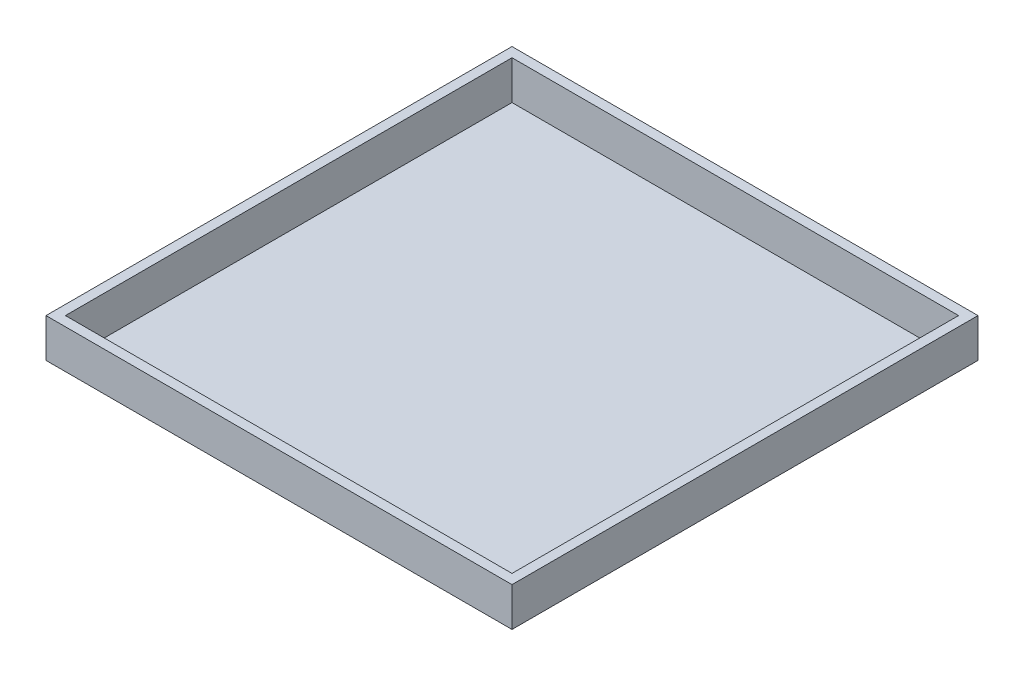
SolidWorks part; units mm, degrees
ref_plane "Front Plane" through (0, 0, 0) normal (0, 0, 1) x (1, 0, 0)
ref_plane "Top Plane" through (0, 0, 0) normal (0, 1, 0) x (1, 0, 0)
ref_plane "Right Plane" through (0, 0, 0) normal (1, 0, 0) x (0, 0, -1)
sketch "Sketch1" plane through (0, 0, 0) normal (0, 1, 0) x (1, 0, 0)
  line L1 (0, 0) -> (2400, 0)
  line L2 (0, 0) -> (0, 2400)
  line L3 (0, 2400) -> (2400, 2400)
  line L4 (2400, 0) -> (2400, 2400)
  dimension "D1" = 2400
  dimension "D2" = 2400
extrude "Boss-Extrude1" add sketch "Sketch1" along normal blind 0.1 contours L4 L3 L2 L1
sketch "Sketch2" plane through (0, 0.1, 0) normal (0, 1, 0) x (1, 0, 0)
  line L0 (50, 2350) -> (50, 50)
  line L1 (0, 2400) -> (2400, 2400)
  line L2 (0, 2400) -> (0, 0)
  line L3 (0, 0) -> (2400, 0)
  line L4 (2400, 2400) -> (2400, 0)
  line L5 (50, 50) -> (2350, 50)
  line L6 (2350, 2350) -> (2350, 50)
  line L7 (50, 2350) -> (2350, 2350)
  dimension "D1" = 50
extrude "Boss-Extrude3" add sketch "Sketch2" along normal blind 200 separate body
sketch "Sketch3" plane through (0, 0.1, 0) normal (0, 1, 0) x (1, 0, 0)
  line L0 (50, 2350) -> (2350, 2350)
  line L1 (2350, 2350) -> (2350, 50)
  line L2 (2350, 50) -> (50, 50)
  line L3 (50, 50) -> (50, 2350)
  line L4 (510, 2350) -> (510, 50)
  line L5 (970, 2350) -> (970, 50)
  line L6 (1430, 2350) -> (1430, 50)
  line L7 (1890, 2350) -> (1890, 50)
  line L8 (2350, 2350) -> (2350, 50)
  line L9 (510, 2350) -> (970, 2350) construction
  line L10 (50, 1890) -> (2350, 1890)
  line L11 (60, 1890) -> (2360, 1890)
  line L12 (60, 1430) -> (2360, 1430)
  line L13 (60, 970) -> (2360, 970)
  line L14 (60, 510) -> (2360, 510)
  line L15 (60, 50) -> (2360, 50)
  line L16 (50, 1430) -> (2350, 1430)
  line L17 (50, 970) -> (2350, 970)
  line L18 (50, 510) -> (2350, 510)
  line L19 (50, 50) -> (2350, 50)
  line L20 (165, 2260) -> (165, 2210)
  line L21 (140, 2235) -> (190, 2235)
  line L22 (280, 2260) -> (280, 2210)
  line L23 (255, 2235) -> (305, 2235)
  line L24 (395, 2260) -> (395, 2210)
  line L25 (370, 2235) -> (420, 2235)
  line L26 (510, 2260) -> (510, 2210)
  line L27 (485, 2235) -> (535, 2235)
  line L28 (625, 2260) -> (625, 2210)
  line L29 (600, 2235) -> (650, 2235)
  line L30 (740, 2260) -> (740, 2210)
  line L31 (715, 2235) -> (765, 2235)
  line L32 (855, 2260) -> (855, 2210)
  line L33 (830, 2235) -> (880, 2235)
  line L34 (970, 2260) -> (970, 2210)
  line L35 (945, 2235) -> (995, 2235)
  line L36 (1085, 2260) -> (1085, 2210)
  line L37 (1060, 2235) -> (1110, 2235)
  line L38 (1200, 2260) -> (1200, 2210)
  line L39 (1175, 2235) -> (1225, 2235)
  line L40 (1315, 2260) -> (1315, 2210)
  line L41 (1290, 2235) -> (1340, 2235)
  line L42 (1430, 2260) -> (1430, 2210)
  line L43 (1405, 2235) -> (1455, 2235)
  line L44 (1545, 2260) -> (1545, 2210)
  line L45 (1520, 2235) -> (1570, 2235)
  line L46 (1660, 2260) -> (1660, 2210)
  line L47 (1635, 2235) -> (1685, 2235)
  line L48 (1775, 2260) -> (1775, 2210)
  line L49 (1750, 2235) -> (1800, 2235)
  line L50 (1890, 2260) -> (1890, 2210)
  line L51 (1865, 2235) -> (1915, 2235)
  line L52 (2005, 2260) -> (2005, 2210)
  line L53 (1980, 2235) -> (2030, 2235)
  line L54 (2120, 2260) -> (2120, 2210)
  line L55 (2095, 2235) -> (2145, 2235)
  line L56 (2235, 2260) -> (2235, 2210)
  line L57 (2210, 2235) -> (2260, 2235)
  line L58 (280, 2145) -> (280, 2095)
  line L59 (255, 2120) -> (305, 2120)
  line L60 (395, 2145) -> (395, 2095)
  line L61 (370, 2120) -> (420, 2120)
  line L62 (510, 2145) -> (510, 2095)
  line L63 (485, 2120) -> (535, 2120)
  line L64 (625, 2145) -> (625, 2095)
  line L65 (600, 2120) -> (650, 2120)
  line L66 (740, 2145) -> (740, 2095)
  line L67 (715, 2120) -> (765, 2120)
  line L68 (855, 2145) -> (855, 2095)
  line L69 (830, 2120) -> (880, 2120)
  line L70 (970, 2145) -> (970, 2095)
  line L71 (945, 2120) -> (995, 2120)
  line L72 (1085, 2145) -> (1085, 2095)
  line L73 (1060, 2120) -> (1110, 2120)
  line L74 (1200, 2145) -> (1200, 2095)
  line L75 (1175, 2120) -> (1225, 2120)
  line L76 (1315, 2145) -> (1315, 2095)
  line L77 (1290, 2120) -> (1340, 2120)
  line L78 (1430, 2145) -> (1430, 2095)
  line L79 (1405, 2120) -> (1455, 2120)
  line L80 (1545, 2145) -> (1545, 2095)
  line L81 (1520, 2120) -> (1570, 2120)
  line L82 (1660, 2145) -> (1660, 2095)
  line L83 (1635, 2120) -> (1685, 2120)
  line L84 (1775, 2145) -> (1775, 2095)
  line L85 (1750, 2120) -> (1800, 2120)
  line L86 (1890, 2145) -> (1890, 2095)
  line L87 (1865, 2120) -> (1915, 2120)
  line L88 (2005, 2145) -> (2005, 2095)
  line L89 (1980, 2120) -> (2030, 2120)
  line L90 (2120, 2145) -> (2120, 2095)
  line L91 (2095, 2120) -> (2145, 2120)
  line L92 (2235, 2145) -> (2235, 2095)
  line L93 (2210, 2120) -> (2260, 2120)
  line L94 (280, 2030) -> (280, 1980)
  line L95 (255, 2005) -> (305, 2005)
  line L96 (395, 2030) -> (395, 1980)
  line L97 (370, 2005) -> (420, 2005)
  line L98 (510, 2030) -> (510, 1980)
  line L99 (485, 2005) -> (535, 2005)
  line L100 (625, 2030) -> (625, 1980)
  line L101 (600, 2005) -> (650, 2005)
  line L102 (740, 2030) -> (740, 1980)
  line L103 (715, 2005) -> (765, 2005)
  line L104 (855, 2030) -> (855, 1980)
  line L105 (830, 2005) -> (880, 2005)
  line L106 (970, 2030) -> (970, 1980)
  line L107 (945, 2005) -> (995, 2005)
  line L108 (1085, 2030) -> (1085, 1980)
  line L109 (1060, 2005) -> (1110, 2005)
  line L110 (1200, 2030) -> (1200, 1980)
  line L111 (1175, 2005) -> (1225, 2005)
  line L112 (1315, 2030) -> (1315, 1980)
  line L113 (1290, 2005) -> (1340, 2005)
  line L114 (1430, 2030) -> (1430, 1980)
  line L115 (1405, 2005) -> (1455, 2005)
  line L116 (1545, 2030) -> (1545, 1980)
  line L117 (1520, 2005) -> (1570, 2005)
  line L118 (1660, 2030) -> (1660, 1980)
  line L119 (1635, 2005) -> (1685, 2005)
  line L120 (1775, 2030) -> (1775, 1980)
  line L121 (1750, 2005) -> (1800, 2005)
  line L122 (1890, 2030) -> (1890, 1980)
  line L123 (1865, 2005) -> (1915, 2005)
  line L124 (2005, 2030) -> (2005, 1980)
  line L125 (1980, 2005) -> (2030, 2005)
  line L126 (2120, 2030) -> (2120, 1980)
  line L127 (2095, 2005) -> (2145, 2005)
  line L128 (2235, 2030) -> (2235, 1980)
  line L129 (2210, 2005) -> (2260, 2005)
  line L130 (280, 1915) -> (280, 1865)
  line L131 (255, 1890) -> (305, 1890)
  line L132 (395, 1915) -> (395, 1865)
  line L133 (370, 1890) -> (420, 1890)
  line L134 (510, 1915) -> (510, 1865)
  line L135 (485, 1890) -> (535, 1890)
  line L136 (625, 1915) -> (625, 1865)
  line L137 (600, 1890) -> (650, 1890)
  line L138 (740, 1915) -> (740, 1865)
  line L139 (715, 1890) -> (765, 1890)
  line L140 (855, 1915) -> (855, 1865)
  line L141 (830, 1890) -> (880, 1890)
  line L142 (970, 1915) -> (970, 1865)
  line L143 (945, 1890) -> (995, 1890)
  line L144 (1085, 1915) -> (1085, 1865)
  line L145 (1060, 1890) -> (1110, 1890)
  line L146 (1200, 1915) -> (1200, 1865)
  line L147 (1175, 1890) -> (1225, 1890)
  line L148 (1315, 1915) -> (1315, 1865)
  line L149 (1290, 1890) -> (1340, 1890)
  line L150 (1430, 1915) -> (1430, 1865)
  line L151 (1405, 1890) -> (1455, 1890)
  line L152 (1545, 1915) -> (1545, 1865)
  line L153 (1520, 1890) -> (1570, 1890)
  line L154 (1660, 1915) -> (1660, 1865)
  line L155 (1635, 1890) -> (1685, 1890)
  line L156 (1775, 1915) -> (1775, 1865)
  line L157 (1750, 1890) -> (1800, 1890)
  line L158 (1890, 1915) -> (1890, 1865)
  line L159 (1865, 1890) -> (1915, 1890)
  line L160 (2005, 1915) -> (2005, 1865)
  line L161 (1980, 1890) -> (2030, 1890)
  line L162 (2120, 1915) -> (2120, 1865)
  line L163 (2095, 1890) -> (2145, 1890)
  line L164 (2235, 1915) -> (2235, 1865)
  line L165 (2210, 1890) -> (2260, 1890)
  line L166 (280, 1800) -> (280, 1750)
  line L167 (255, 1775) -> (305, 1775)
  line L168 (395, 1800) -> (395, 1750)
  line L169 (370, 1775) -> (420, 1775)
  line L170 (510, 1800) -> (510, 1750)
  line L171 (485, 1775) -> (535, 1775)
  line L172 (625, 1800) -> (625, 1750)
  line L173 (600, 1775) -> (650, 1775)
  line L174 (740, 1800) -> (740, 1750)
  line L175 (715, 1775) -> (765, 1775)
  line L176 (855, 1800) -> (855, 1750)
  line L177 (830, 1775) -> (880, 1775)
  line L178 (970, 1800) -> (970, 1750)
  line L179 (945, 1775) -> (995, 1775)
  line L180 (1085, 1800) -> (1085, 1750)
  line L181 (1060, 1775) -> (1110, 1775)
  line L182 (1200, 1800) -> (1200, 1750)
  line L183 (1175, 1775) -> (1225, 1775)
  line L184 (1315, 1800) -> (1315, 1750)
  line L185 (1290, 1775) -> (1340, 1775)
  line L186 (1430, 1800) -> (1430, 1750)
  line L187 (1405, 1775) -> (1455, 1775)
  line L188 (1545, 1800) -> (1545, 1750)
  line L189 (1520, 1775) -> (1570, 1775)
  line L190 (1660, 1800) -> (1660, 1750)
  line L191 (1635, 1775) -> (1685, 1775)
  line L192 (1775, 1800) -> (1775, 1750)
  line L193 (1750, 1775) -> (1800, 1775)
  line L194 (1890, 1800) -> (1890, 1750)
  line L195 (1865, 1775) -> (1915, 1775)
  line L196 (2005, 1800) -> (2005, 1750)
  line L197 (1980, 1775) -> (2030, 1775)
  line L198 (2120, 1800) -> (2120, 1750)
  line L199 (2095, 1775) -> (2145, 1775)
  line L200 (2235, 1800) -> (2235, 1750)
  line L201 (2210, 1775) -> (2260, 1775)
  line L202 (280, 1685) -> (280, 1635)
  line L203 (255, 1660) -> (305, 1660)
  line L204 (395, 1685) -> (395, 1635)
  line L205 (370, 1660) -> (420, 1660)
  line L206 (510, 1685) -> (510, 1635)
  line L207 (485, 1660) -> (535, 1660)
  line L208 (625, 1685) -> (625, 1635)
  line L209 (600, 1660) -> (650, 1660)
  line L210 (740, 1685) -> (740, 1635)
  line L211 (715, 1660) -> (765, 1660)
  line L212 (855, 1685) -> (855, 1635)
  line L213 (830, 1660) -> (880, 1660)
  line L214 (970, 1685) -> (970, 1635)
  line L215 (945, 1660) -> (995, 1660)
  line L216 (1085, 1685) -> (1085, 1635)
  line L217 (1060, 1660) -> (1110, 1660)
  line L218 (1200, 1685) -> (1200, 1635)
  line L219 (1175, 1660) -> (1225, 1660)
  line L220 (1315, 1685) -> (1315, 1635)
  line L221 (1290, 1660) -> (1340, 1660)
  line L222 (1430, 1685) -> (1430, 1635)
  line L223 (1405, 1660) -> (1455, 1660)
  line L224 (1545, 1685) -> (1545, 1635)
  line L225 (1520, 1660) -> (1570, 1660)
  line L226 (1660, 1685) -> (1660, 1635)
  line L227 (1635, 1660) -> (1685, 1660)
  line L228 (1775, 1685) -> (1775, 1635)
  line L229 (1750, 1660) -> (1800, 1660)
  line L230 (1890, 1685) -> (1890, 1635)
  line L231 (1865, 1660) -> (1915, 1660)
  line L232 (2005, 1685) -> (2005, 1635)
  line L233 (1980, 1660) -> (2030, 1660)
  line L234 (2120, 1685) -> (2120, 1635)
  line L235 (2095, 1660) -> (2145, 1660)
  line L236 (2235, 1685) -> (2235, 1635)
  line L237 (2210, 1660) -> (2260, 1660)
  line L238 (280, 1570) -> (280, 1520)
  line L239 (255, 1545) -> (305, 1545)
  line L240 (395, 1570) -> (395, 1520)
  line L241 (370, 1545) -> (420, 1545)
  line L242 (510, 1570) -> (510, 1520)
  line L243 (485, 1545) -> (535, 1545)
  line L244 (625, 1570) -> (625, 1520)
  line L245 (600, 1545) -> (650, 1545)
  line L246 (740, 1570) -> (740, 1520)
  line L247 (715, 1545) -> (765, 1545)
  line L248 (855, 1570) -> (855, 1520)
  line L249 (830, 1545) -> (880, 1545)
  line L250 (970, 1570) -> (970, 1520)
  line L251 (945, 1545) -> (995, 1545)
  line L252 (1085, 1570) -> (1085, 1520)
  line L253 (1060, 1545) -> (1110, 1545)
  line L254 (1200, 1570) -> (1200, 1520)
  line L255 (1175, 1545) -> (1225, 1545)
  line L256 (1315, 1570) -> (1315, 1520)
  line L257 (1290, 1545) -> (1340, 1545)
  line L258 (1430, 1570) -> (1430, 1520)
  line L259 (1405, 1545) -> (1455, 1545)
  line L260 (1545, 1570) -> (1545, 1520)
  line L261 (1520, 1545) -> (1570, 1545)
  line L262 (1660, 1570) -> (1660, 1520)
  line L263 (1635, 1545) -> (1685, 1545)
  line L264 (1775, 1570) -> (1775, 1520)
  line L265 (1750, 1545) -> (1800, 1545)
  line L266 (1890, 1570) -> (1890, 1520)
  line L267 (1865, 1545) -> (1915, 1545)
  line L268 (2005, 1570) -> (2005, 1520)
  line L269 (1980, 1545) -> (2030, 1545)
  line L270 (2120, 1570) -> (2120, 1520)
  line L271 (2095, 1545) -> (2145, 1545)
  line L272 (2235, 1570) -> (2235, 1520)
  line L273 (2210, 1545) -> (2260, 1545)
  line L274 (280, 1455) -> (280, 1405)
  line L275 (255, 1430) -> (305, 1430)
  line L276 (395, 1455) -> (395, 1405)
  line L277 (370, 1430) -> (420, 1430)
  line L278 (510, 1455) -> (510, 1405)
  line L279 (485, 1430) -> (535, 1430)
  line L280 (625, 1455) -> (625, 1405)
  line L281 (600, 1430) -> (650, 1430)
  line L282 (740, 1455) -> (740, 1405)
  line L283 (715, 1430) -> (765, 1430)
  line L284 (855, 1455) -> (855, 1405)
  line L285 (830, 1430) -> (880, 1430)
  line L286 (970, 1455) -> (970, 1405)
  line L287 (945, 1430) -> (995, 1430)
  line L288 (1085, 1455) -> (1085, 1405)
  line L289 (1060, 1430) -> (1110, 1430)
  line L290 (1200, 1455) -> (1200, 1405)
  line L291 (1175, 1430) -> (1225, 1430)
  line L292 (1315, 1455) -> (1315, 1405)
  line L293 (1290, 1430) -> (1340, 1430)
  line L294 (1430, 1455) -> (1430, 1405)
  line L295 (1405, 1430) -> (1455, 1430)
  line L296 (1545, 1455) -> (1545, 1405)
  line L297 (1520, 1430) -> (1570, 1430)
  line L298 (1660, 1455) -> (1660, 1405)
  line L299 (1635, 1430) -> (1685, 1430)
  line L300 (1775, 1455) -> (1775, 1405)
  line L301 (1750, 1430) -> (1800, 1430)
  line L302 (1890, 1455) -> (1890, 1405)
  line L303 (1865, 1430) -> (1915, 1430)
  line L304 (2005, 1455) -> (2005, 1405)
  line L305 (1980, 1430) -> (2030, 1430)
  line L306 (2120, 1455) -> (2120, 1405)
  line L307 (2095, 1430) -> (2145, 1430)
  line L308 (2235, 1455) -> (2235, 1405)
  line L309 (2210, 1430) -> (2260, 1430)
  line L310 (280, 1340) -> (280, 1290)
  line L311 (255, 1315) -> (305, 1315)
  line L312 (395, 1340) -> (395, 1290)
  line L313 (370, 1315) -> (420, 1315)
  line L314 (510, 1340) -> (510, 1290)
  line L315 (485, 1315) -> (535, 1315)
  line L316 (625, 1340) -> (625, 1290)
  line L317 (600, 1315) -> (650, 1315)
  line L318 (740, 1340) -> (740, 1290)
  line L319 (715, 1315) -> (765, 1315)
  line L320 (855, 1340) -> (855, 1290)
  line L321 (830, 1315) -> (880, 1315)
  line L322 (970, 1340) -> (970, 1290)
  line L323 (945, 1315) -> (995, 1315)
  line L324 (1085, 1340) -> (1085, 1290)
  line L325 (1060, 1315) -> (1110, 1315)
  line L326 (1200, 1340) -> (1200, 1290)
  line L327 (1175, 1315) -> (1225, 1315)
  line L328 (1315, 1340) -> (1315, 1290)
  line L329 (1290, 1315) -> (1340, 1315)
  line L330 (1430, 1340) -> (1430, 1290)
  line L331 (1405, 1315) -> (1455, 1315)
  line L332 (1545, 1340) -> (1545, 1290)
  line L333 (1520, 1315) -> (1570, 1315)
  line L334 (1660, 1340) -> (1660, 1290)
  line L335 (1635, 1315) -> (1685, 1315)
  line L336 (1775, 1340) -> (1775, 1290)
  line L337 (1750, 1315) -> (1800, 1315)
  line L338 (1890, 1340) -> (1890, 1290)
  line L339 (1865, 1315) -> (1915, 1315)
  line L340 (2005, 1340) -> (2005, 1290)
  line L341 (1980, 1315) -> (2030, 1315)
  line L342 (2120, 1340) -> (2120, 1290)
  line L343 (2095, 1315) -> (2145, 1315)
  line L344 (2235, 1340) -> (2235, 1290)
  line L345 (2210, 1315) -> (2260, 1315)
  line L346 (280, 1225) -> (280, 1175)
  line L347 (255, 1200) -> (305, 1200)
  line L348 (395, 1225) -> (395, 1175)
  line L349 (370, 1200) -> (420, 1200)
  line L350 (510, 1225) -> (510, 1175)
  line L351 (485, 1200) -> (535, 1200)
  line L352 (625, 1225) -> (625, 1175)
  line L353 (600, 1200) -> (650, 1200)
  line L354 (740, 1225) -> (740, 1175)
  line L355 (715, 1200) -> (765, 1200)
  line L356 (855, 1225) -> (855, 1175)
  line L357 (830, 1200) -> (880, 1200)
  line L358 (970, 1225) -> (970, 1175)
  line L359 (945, 1200) -> (995, 1200)
  line L360 (1085, 1225) -> (1085, 1175)
  line L361 (1060, 1200) -> (1110, 1200)
  line L362 (1200, 1225) -> (1200, 1175)
  line L363 (1175, 1200) -> (1225, 1200)
  line L364 (1315, 1225) -> (1315, 1175)
  line L365 (1290, 1200) -> (1340, 1200)
  line L366 (1430, 1225) -> (1430, 1175)
  line L367 (1405, 1200) -> (1455, 1200)
  line L368 (1545, 1225) -> (1545, 1175)
  line L369 (1520, 1200) -> (1570, 1200)
  line L370 (1660, 1225) -> (1660, 1175)
  line L371 (1635, 1200) -> (1685, 1200)
  line L372 (1775, 1225) -> (1775, 1175)
  line L373 (1750, 1200) -> (1800, 1200)
  line L374 (1890, 1225) -> (1890, 1175)
  line L375 (1865, 1200) -> (1915, 1200)
  line L376 (2005, 1225) -> (2005, 1175)
  line L377 (1980, 1200) -> (2030, 1200)
  line L378 (2120, 1225) -> (2120, 1175)
  line L379 (2095, 1200) -> (2145, 1200)
  line L380 (2235, 1225) -> (2235, 1175)
  line L381 (2210, 1200) -> (2260, 1200)
  line L382 (280, 1110) -> (280, 1060)
  line L383 (255, 1085) -> (305, 1085)
  line L384 (395, 1110) -> (395, 1060)
  line L385 (370, 1085) -> (420, 1085)
  line L386 (510, 1110) -> (510, 1060)
  line L387 (485, 1085) -> (535, 1085)
  line L388 (625, 1110) -> (625, 1060)
  line L389 (600, 1085) -> (650, 1085)
  line L390 (740, 1110) -> (740, 1060)
  line L391 (715, 1085) -> (765, 1085)
  line L392 (855, 1110) -> (855, 1060)
  line L393 (830, 1085) -> (880, 1085)
  line L394 (970, 1110) -> (970, 1060)
  line L395 (945, 1085) -> (995, 1085)
  line L396 (1085, 1110) -> (1085, 1060)
  line L397 (1060, 1085) -> (1110, 1085)
  line L398 (1200, 1110) -> (1200, 1060)
  line L399 (1175, 1085) -> (1225, 1085)
  line L400 (1315, 1110) -> (1315, 1060)
  line L401 (1290, 1085) -> (1340, 1085)
  line L402 (1430, 1110) -> (1430, 1060)
  line L403 (1405, 1085) -> (1455, 1085)
  line L404 (1545, 1110) -> (1545, 1060)
  line L405 (1520, 1085) -> (1570, 1085)
  line L406 (1660, 1110) -> (1660, 1060)
  line L407 (1635, 1085) -> (1685, 1085)
  line L408 (1775, 1110) -> (1775, 1060)
  line L409 (1750, 1085) -> (1800, 1085)
  line L410 (1890, 1110) -> (1890, 1060)
  line L411 (1865, 1085) -> (1915, 1085)
  line L412 (2005, 1110) -> (2005, 1060)
  line L413 (1980, 1085) -> (2030, 1085)
  line L414 (2120, 1110) -> (2120, 1060)
  line L415 (2095, 1085) -> (2145, 1085)
  line L416 (2235, 1110) -> (2235, 1060)
  line L417 (2210, 1085) -> (2260, 1085)
  line L418 (280, 995) -> (280, 945)
  line L419 (255, 970) -> (305, 970)
  line L420 (395, 995) -> (395, 945)
  line L421 (370, 970) -> (420, 970)
  line L422 (510, 995) -> (510, 945)
  line L423 (485, 970) -> (535, 970)
  line L424 (625, 995) -> (625, 945)
  line L425 (600, 970) -> (650, 970)
  line L426 (740, 995) -> (740, 945)
  line L427 (715, 970) -> (765, 970)
  line L428 (855, 995) -> (855, 945)
  line L429 (830, 970) -> (880, 970)
  line L430 (970, 995) -> (970, 945)
  line L431 (945, 970) -> (995, 970)
  line L432 (1085, 995) -> (1085, 945)
  line L433 (1060, 970) -> (1110, 970)
  line L434 (1200, 995) -> (1200, 945)
  line L435 (1175, 970) -> (1225, 970)
  line L436 (1315, 995) -> (1315, 945)
  line L437 (1290, 970) -> (1340, 970)
  line L438 (1430, 995) -> (1430, 945)
  line L439 (1405, 970) -> (1455, 970)
  line L440 (1545, 995) -> (1545, 945)
  line L441 (1520, 970) -> (1570, 970)
  line L442 (1660, 995) -> (1660, 945)
  line L443 (1635, 970) -> (1685, 970)
  line L444 (1775, 995) -> (1775, 945)
  line L445 (1750, 970) -> (1800, 970)
  line L446 (1890, 995) -> (1890, 945)
  line L447 (1865, 970) -> (1915, 970)
  line L448 (2005, 995) -> (2005, 945)
  line L449 (1980, 970) -> (2030, 970)
  line L450 (2120, 995) -> (2120, 945)
  line L451 (2095, 970) -> (2145, 970)
  line L452 (2235, 995) -> (2235, 945)
  line L453 (2210, 970) -> (2260, 970)
  line L454 (280, 880) -> (280, 830)
  line L455 (255, 855) -> (305, 855)
  line L456 (395, 880) -> (395, 830)
  line L457 (370, 855) -> (420, 855)
  line L458 (510, 880) -> (510, 830)
  line L459 (485, 855) -> (535, 855)
  line L460 (625, 880) -> (625, 830)
  line L461 (600, 855) -> (650, 855)
  line L462 (740, 880) -> (740, 830)
  line L463 (715, 855) -> (765, 855)
  line L464 (855, 880) -> (855, 830)
  line L465 (830, 855) -> (880, 855)
  line L466 (970, 880) -> (970, 830)
  line L467 (945, 855) -> (995, 855)
  line L468 (1085, 880) -> (1085, 830)
  line L469 (1060, 855) -> (1110, 855)
  line L470 (1200, 880) -> (1200, 830)
  line L471 (1175, 855) -> (1225, 855)
  line L472 (1315, 880) -> (1315, 830)
  line L473 (1290, 855) -> (1340, 855)
  line L474 (1430, 880) -> (1430, 830)
  line L475 (1405, 855) -> (1455, 855)
  line L476 (1545, 880) -> (1545, 830)
  line L477 (1520, 855) -> (1570, 855)
  line L478 (1660, 880) -> (1660, 830)
  line L479 (1635, 855) -> (1685, 855)
  line L480 (1775, 880) -> (1775, 830)
  line L481 (1750, 855) -> (1800, 855)
  line L482 (1890, 880) -> (1890, 830)
  line L483 (1865, 855) -> (1915, 855)
  line L484 (2005, 880) -> (2005, 830)
  line L485 (1980, 855) -> (2030, 855)
  line L486 (2120, 880) -> (2120, 830)
  line L487 (2095, 855) -> (2145, 855)
  line L488 (2235, 880) -> (2235, 830)
  line L489 (2210, 855) -> (2260, 855)
  line L490 (280, 765) -> (280, 715)
  line L491 (255, 740) -> (305, 740)
  line L492 (395, 765) -> (395, 715)
  line L493 (370, 740) -> (420, 740)
  line L494 (510, 765) -> (510, 715)
  line L495 (485, 740) -> (535, 740)
  line L496 (625, 765) -> (625, 715)
  line L497 (600, 740) -> (650, 740)
  line L498 (740, 765) -> (740, 715)
  line L499 (715, 740) -> (765, 740)
  line L500 (855, 765) -> (855, 715)
  line L501 (830, 740) -> (880, 740)
  line L502 (970, 765) -> (970, 715)
  line L503 (945, 740) -> (995, 740)
  line L504 (1085, 765) -> (1085, 715)
  line L505 (1060, 740) -> (1110, 740)
  line L506 (1200, 765) -> (1200, 715)
  line L507 (1175, 740) -> (1225, 740)
  line L508 (1315, 765) -> (1315, 715)
  line L509 (1290, 740) -> (1340, 740)
  line L510 (1430, 765) -> (1430, 715)
  line L511 (1405, 740) -> (1455, 740)
  line L512 (1545, 765) -> (1545, 715)
  line L513 (1520, 740) -> (1570, 740)
  line L514 (1660, 765) -> (1660, 715)
  line L515 (1635, 740) -> (1685, 740)
  line L516 (1775, 765) -> (1775, 715)
  line L517 (1750, 740) -> (1800, 740)
  line L518 (1890, 765) -> (1890, 715)
  line L519 (1865, 740) -> (1915, 740)
  line L520 (2005, 765) -> (2005, 715)
  line L521 (1980, 740) -> (2030, 740)
  line L522 (2120, 765) -> (2120, 715)
  line L523 (2095, 740) -> (2145, 740)
  line L524 (2235, 765) -> (2235, 715)
  line L525 (2210, 740) -> (2260, 740)
  line L526 (280, 650) -> (280, 600)
  line L527 (255, 625) -> (305, 625)
  line L528 (395, 650) -> (395, 600)
  line L529 (370, 625) -> (420, 625)
  line L530 (510, 650) -> (510, 600)
  line L531 (485, 625) -> (535, 625)
  line L532 (625, 650) -> (625, 600)
  line L533 (600, 625) -> (650, 625)
  line L534 (740, 650) -> (740, 600)
  line L535 (715, 625) -> (765, 625)
  line L536 (855, 650) -> (855, 600)
  line L537 (830, 625) -> (880, 625)
  line L538 (970, 650) -> (970, 600)
  line L539 (945, 625) -> (995, 625)
  line L540 (1085, 650) -> (1085, 600)
  line L541 (1060, 625) -> (1110, 625)
  line L542 (1200, 650) -> (1200, 600)
  line L543 (1175, 625) -> (1225, 625)
  line L544 (1315, 650) -> (1315, 600)
  line L545 (1290, 625) -> (1340, 625)
  line L546 (1430, 650) -> (1430, 600)
  line L547 (1405, 625) -> (1455, 625)
  line L548 (1545, 650) -> (1545, 600)
  line L549 (1520, 625) -> (1570, 625)
  line L550 (1660, 650) -> (1660, 600)
  line L551 (1635, 625) -> (1685, 625)
  line L552 (1775, 650) -> (1775, 600)
  line L553 (1750, 625) -> (1800, 625)
  line L554 (1890, 650) -> (1890, 600)
  line L555 (1865, 625) -> (1915, 625)
  line L556 (2005, 650) -> (2005, 600)
  line L557 (1980, 625) -> (2030, 625)
  line L558 (2120, 650) -> (2120, 600)
  line L559 (2095, 625) -> (2145, 625)
  line L560 (2235, 650) -> (2235, 600)
  line L561 (2210, 625) -> (2260, 625)
  line L562 (280, 535) -> (280, 485)
  line L563 (255, 510) -> (305, 510)
  line L564 (395, 535) -> (395, 485)
  line L565 (370, 510) -> (420, 510)
  line L566 (510, 535) -> (510, 485)
  line L567 (485, 510) -> (535, 510)
  line L568 (625, 535) -> (625, 485)
  line L569 (600, 510) -> (650, 510)
  line L570 (740, 535) -> (740, 485)
  line L571 (715, 510) -> (765, 510)
  line L572 (855, 535) -> (855, 485)
  line L573 (830, 510) -> (880, 510)
  line L574 (970, 535) -> (970, 485)
  line L575 (945, 510) -> (995, 510)
  line L576 (1085, 535) -> (1085, 485)
  line L577 (1060, 510) -> (1110, 510)
  line L578 (1200, 535) -> (1200, 485)
  line L579 (1175, 510) -> (1225, 510)
  line L580 (1315, 535) -> (1315, 485)
  line L581 (1290, 510) -> (1340, 510)
  line L582 (1430, 535) -> (1430, 485)
  line L583 (1405, 510) -> (1455, 510)
  line L584 (1545, 535) -> (1545, 485)
  line L585 (1520, 510) -> (1570, 510)
  line L586 (1660, 535) -> (1660, 485)
  line L587 (1635, 510) -> (1685, 510)
  line L588 (1775, 535) -> (1775, 485)
  line L589 (1750, 510) -> (1800, 510)
  line L590 (1890, 535) -> (1890, 485)
  line L591 (1865, 510) -> (1915, 510)
  line L592 (2005, 535) -> (2005, 485)
  line L593 (1980, 510) -> (2030, 510)
  line L594 (2120, 535) -> (2120, 485)
  line L595 (2095, 510) -> (2145, 510)
  line L596 (2235, 535) -> (2235, 485)
  line L597 (2210, 510) -> (2260, 510)
  line L598 (280, 420) -> (280, 370)
  line L599 (255, 395) -> (305, 395)
  line L600 (395, 420) -> (395, 370)
  line L601 (370, 395) -> (420, 395)
  line L602 (510, 420) -> (510, 370)
  line L603 (485, 395) -> (535, 395)
  line L604 (625, 420) -> (625, 370)
  line L605 (600, 395) -> (650, 395)
  line L606 (740, 420) -> (740, 370)
  line L607 (715, 395) -> (765, 395)
  line L608 (855, 420) -> (855, 370)
  line L609 (830, 395) -> (880, 395)
  line L610 (970, 420) -> (970, 370)
  line L611 (945, 395) -> (995, 395)
  line L612 (1085, 420) -> (1085, 370)
  line L613 (1060, 395) -> (1110, 395)
  line L614 (1200, 420) -> (1200, 370)
  line L615 (1175, 395) -> (1225, 395)
  line L616 (1315, 420) -> (1315, 370)
  line L617 (1290, 395) -> (1340, 395)
  line L618 (1430, 420) -> (1430, 370)
  line L619 (1405, 395) -> (1455, 395)
  line L620 (1545, 420) -> (1545, 370)
  line L621 (1520, 395) -> (1570, 395)
  line L622 (1660, 420) -> (1660, 370)
  line L623 (1635, 395) -> (1685, 395)
  line L624 (1775, 420) -> (1775, 370)
  line L625 (1750, 395) -> (1800, 395)
  line L626 (1890, 420) -> (1890, 370)
  line L627 (1865, 395) -> (1915, 395)
  line L628 (2005, 420) -> (2005, 370)
  line L629 (1980, 395) -> (2030, 395)
  line L630 (2120, 420) -> (2120, 370)
  line L631 (2095, 395) -> (2145, 395)
  line L632 (2235, 420) -> (2235, 370)
  line L633 (2210, 395) -> (2260, 395)
  line L634 (280, 305) -> (280, 255)
  line L635 (255, 280) -> (305, 280)
  line L636 (395, 305) -> (395, 255)
  line L637 (370, 280) -> (420, 280)
  line L638 (510, 305) -> (510, 255)
  line L639 (485, 280) -> (535, 280)
  line L640 (625, 305) -> (625, 255)
  line L641 (600, 280) -> (650, 280)
  line L642 (740, 305) -> (740, 255)
  line L643 (715, 280) -> (765, 280)
  line L644 (855, 305) -> (855, 255)
  line L645 (830, 280) -> (880, 280)
  line L646 (970, 305) -> (970, 255)
  line L647 (945, 280) -> (995, 280)
  line L648 (1085, 305) -> (1085, 255)
  line L649 (1060, 280) -> (1110, 280)
  line L650 (1200, 305) -> (1200, 255)
  line L651 (1175, 280) -> (1225, 280)
  line L652 (1315, 305) -> (1315, 255)
  line L653 (1290, 280) -> (1340, 280)
  line L654 (1430, 305) -> (1430, 255)
  line L655 (1405, 280) -> (1455, 280)
  line L656 (1545, 305) -> (1545, 255)
  line L657 (1520, 280) -> (1570, 280)
  line L658 (1660, 305) -> (1660, 255)
  line L659 (1635, 280) -> (1685, 280)
  line L660 (1775, 305) -> (1775, 255)
  line L661 (1750, 280) -> (1800, 280)
  line L662 (1890, 305) -> (1890, 255)
  line L663 (1865, 280) -> (1915, 280)
  line L664 (2005, 305) -> (2005, 255)
  line L665 (1980, 280) -> (2030, 280)
  line L666 (2120, 305) -> (2120, 255)
  line L667 (2095, 280) -> (2145, 280)
  line L668 (2235, 305) -> (2235, 255)
  line L669 (2210, 280) -> (2260, 280)
  line L670 (280, 190) -> (280, 140)
  line L671 (255, 165) -> (305, 165)
  line L672 (395, 190) -> (395, 140)
  line L673 (370, 165) -> (420, 165)
  line L674 (510, 190) -> (510, 140)
  line L675 (485, 165) -> (535, 165)
  line L676 (625, 190) -> (625, 140)
  line L677 (600, 165) -> (650, 165)
  line L678 (740, 190) -> (740, 140)
  line L679 (715, 165) -> (765, 165)
  line L680 (855, 190) -> (855, 140)
  line L681 (830, 165) -> (880, 165)
  line L682 (970, 190) -> (970, 140)
  line L683 (945, 165) -> (995, 165)
  line L684 (1085, 190) -> (1085, 140)
  line L685 (1060, 165) -> (1110, 165)
  line L686 (1200, 190) -> (1200, 140)
  line L687 (1175, 165) -> (1225, 165)
  line L688 (1315, 190) -> (1315, 140)
  line L689 (1290, 165) -> (1340, 165)
  line L690 (1430, 190) -> (1430, 140)
  line L691 (1405, 165) -> (1455, 165)
  line L692 (1545, 190) -> (1545, 140)
  line L693 (1520, 165) -> (1570, 165)
  line L694 (1660, 190) -> (1660, 140)
  line L695 (1635, 165) -> (1685, 165)
  line L696 (1775, 190) -> (1775, 140)
  line L697 (1750, 165) -> (1800, 165)
  line L698 (1890, 190) -> (1890, 140)
  line L699 (1865, 165) -> (1915, 165)
  line L700 (2005, 190) -> (2005, 140)
  line L701 (1980, 165) -> (2030, 165)
  line L702 (2120, 190) -> (2120, 140)
  line L703 (2095, 165) -> (2145, 165)
  line L704 (2235, 190) -> (2235, 140)
  line L705 (2210, 165) -> (2260, 165)
  line L706 (165, 2145) -> (165, 2095)
  line L707 (140, 2120) -> (190, 2120)
  line L708 (165, 2030) -> (165, 1980)
  line L709 (140, 2005) -> (190, 2005)
  line L710 (165, 1915) -> (165, 1865)
  line L711 (140, 1890) -> (190, 1890)
  line L712 (165, 1800) -> (165, 1750)
  line L713 (140, 1775) -> (190, 1775)
  line L714 (165, 1685) -> (165, 1635)
  line L715 (140, 1660) -> (190, 1660)
  line L716 (165, 1570) -> (165, 1520)
  line L717 (140, 1545) -> (190, 1545)
  line L718 (165, 1455) -> (165, 1405)
  line L719 (140, 1430) -> (190, 1430)
  line L720 (165, 1340) -> (165, 1290)
  line L721 (140, 1315) -> (190, 1315)
  line L722 (165, 1225) -> (165, 1175)
  line L723 (140, 1200) -> (190, 1200)
  line L724 (165, 1110) -> (165, 1060)
  line L725 (140, 1085) -> (190, 1085)
  line L726 (165, 995) -> (165, 945)
  line L727 (140, 970) -> (190, 970)
  line L728 (165, 880) -> (165, 830)
  line L729 (140, 855) -> (190, 855)
  line L730 (165, 765) -> (165, 715)
  line L731 (140, 740) -> (190, 740)
  line L732 (165, 650) -> (165, 600)
  line L733 (140, 625) -> (190, 625)
  line L734 (165, 535) -> (165, 485)
  line L735 (140, 510) -> (190, 510)
  line L736 (165, 420) -> (165, 370)
  line L737 (140, 395) -> (190, 395)
  line L738 (165, 305) -> (165, 255)
  line L739 (140, 280) -> (190, 280)
  line L740 (165, 190) -> (165, 140)
  line L741 (140, 165) -> (190, 165)
  line L742 (50, 2350) -> (50, 50) construction
  point P23 (510, 1890)
  point P45 (165, 2235)
  dimension "D1" = 460
  dimension "D3" = 460
  dimension "D4" = 460
  dimension "D6" = 50
  dimension "D7" = 50
  dimension "D8" = 115
  dimension "D9" = 115
  dimension "D10" = 65
  dimension "D11" = 65
  dimension "D14" = 115
  dimension "D2" = 5
  dimension "D5" = 5
  dimension "D12" = 19
  dimension "D13" = 19
sketch "Sketch4" plane through (0, 0, 0) normal (0, -1, 0) x (1, 0, 0)
  line L4 (2400, 0) -> (0, 0)
  line L5 (0, 0) -> (0, -2400)
  line L6 (0, -2400) -> (2400, -2400)
  line L7 (2400, -2400) -> (2400, 0)
  line L8 (2400, 0) -> (0, 0)
  line L9 (0, 0) -> (0, -2400)
  line L10 (0, -2400) -> (2400, -2400)
  line L11 (2400, -2400) -> (2400, 0)
  dimension "D1" = 0
